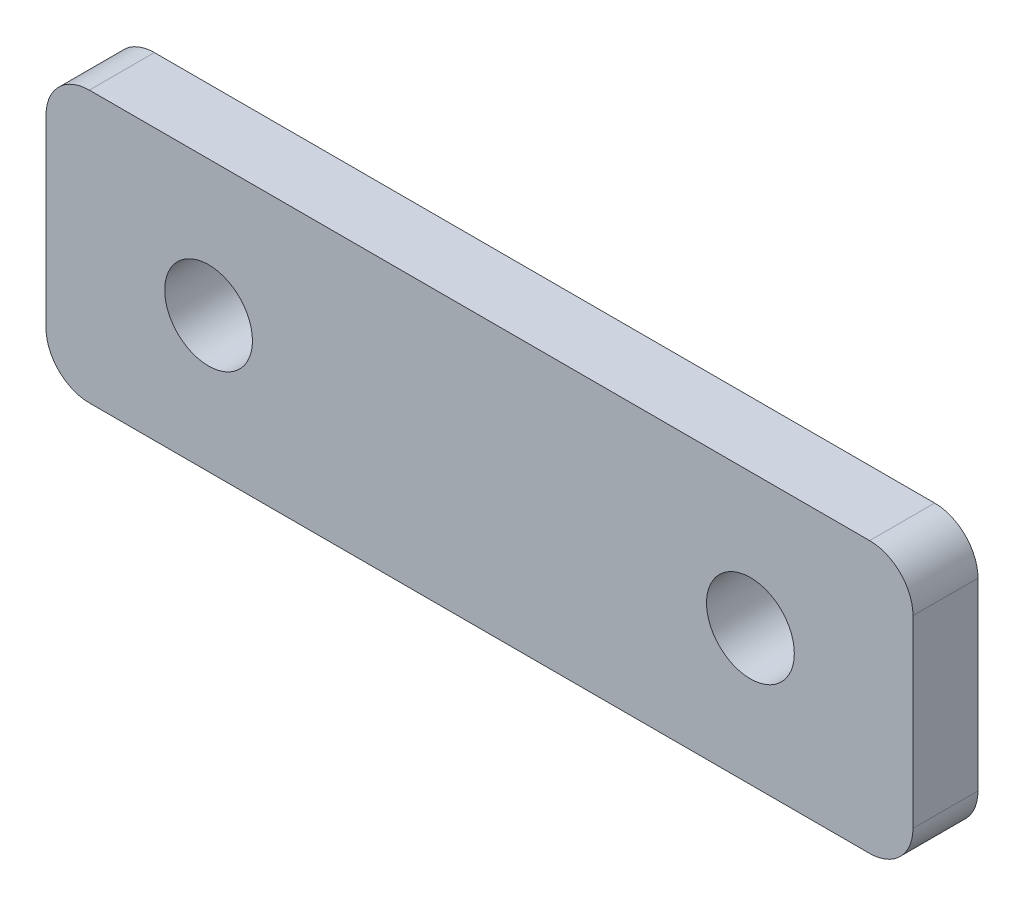
SolidWorks part; units mm, degrees
material "环氧玻璃布层压板"
ref_plane "前视基准面" through (0, 0, 0) normal (0, 0, 1) x (1, 0, 0)
ref_plane "上视基准面" through (0, 0, 0) normal (0, 1, 0) x (1, 0, 0)
ref_plane "右视基准面" through (0, 0, 0) normal (1, 0, 0) x (0, 0, -1)
sketch "草图1" plane through (0, 0, 0) normal (0, 0, 1) x (1, 0, 0)
  line L1 (-20, -6.25) -> (20, -6.25)
  line L2 (-20, -6.25) -> (-20, 6.25)
  line L3 (-20, 6.25) -> (20, 6.25)
  line L4 (20, -6.25) -> (20, 6.25)
  line L5 (0, 6.25) -> (0, -6.25) construction
  line L6 (-20, 0) -> (20, 0) construction
  circle A0 centre (-12.5, 0) radius 2.025
  circle A1 centre (12.5, 0) radius 2.025
  point P0 (0, 0)
  dimension "D4" = 4.05
  dimension "D1" = 40
  dimension "D2" = 12.5
  dimension "D3" = 25
extrude "凸台-拉伸1" add sketch "草图1" along normal mid plane 3
fillet "圆角1" radius 2 4 edges at (-20, -6.25, 0) (-20, 6.25, 0) (20, -6.25, 0) (20, 6.25, 0)
